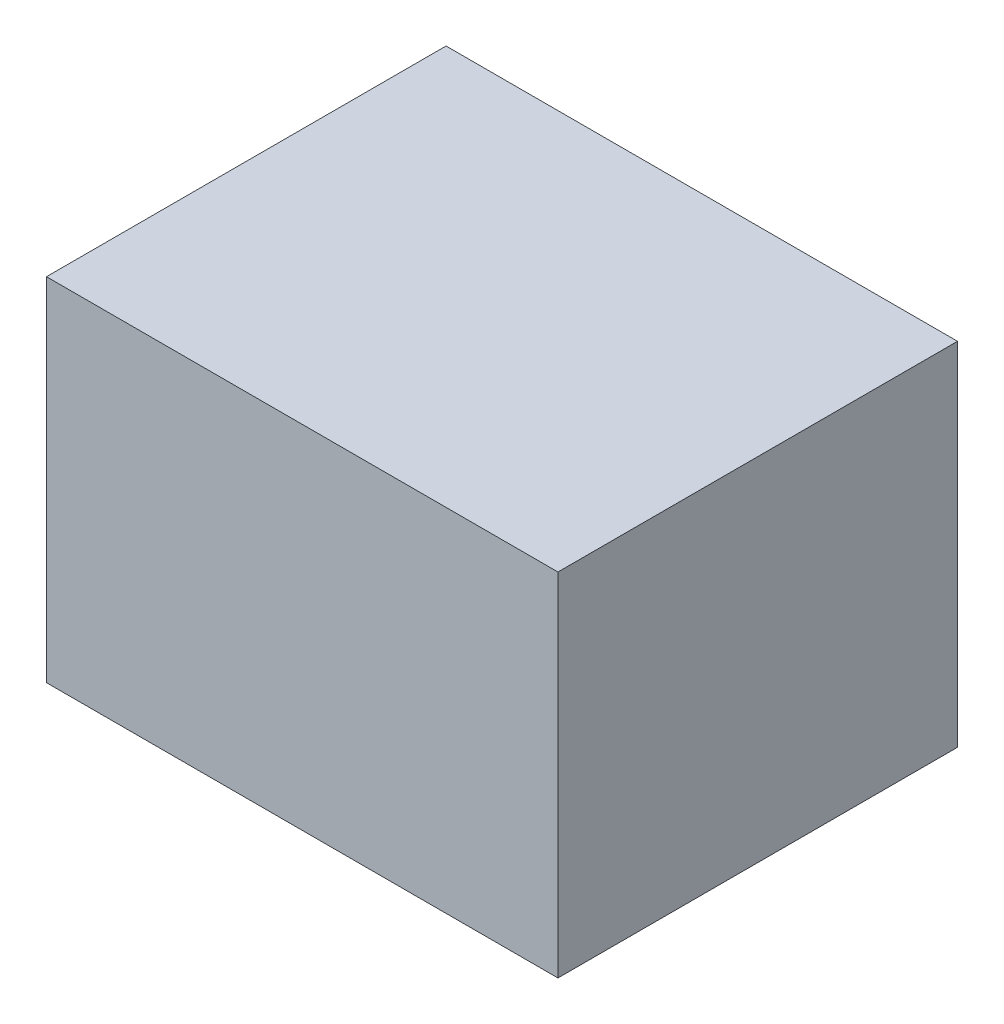
SolidWorks part; units mm, degrees
ref_plane "Front Plane" through (0, 0, 0) normal (0, 0, 1) x (1, 0, 0)
ref_plane "Top Plane" through (0, 0, 0) normal (0, 1, 0) x (1, 0, 0)
ref_plane "Right Plane" through (0, 0, 0) normal (1, 0, 0) x (0, 0, -1)
sketch "Sketch1" plane through (0, 0, 0) normal (0, 1, 0) x (1, 0, 0)
  line L1 (-203.2, -158.75) -> (203.2, -158.75)
  line L2 (-203.2, -158.75) -> (-203.2, 158.75)
  line L3 (-203.2, 158.75) -> (203.2, 158.75)
  line L4 (203.2, -158.75) -> (203.2, 158.75)
  point P4 (0, 158.75)
  point P6 (203.2, 0)
  dimension "D1" = 406.4
  dimension "D2" = 317.5
extrude "Boss-Extrude1" add sketch "Sketch1" along normal blind 279.4
